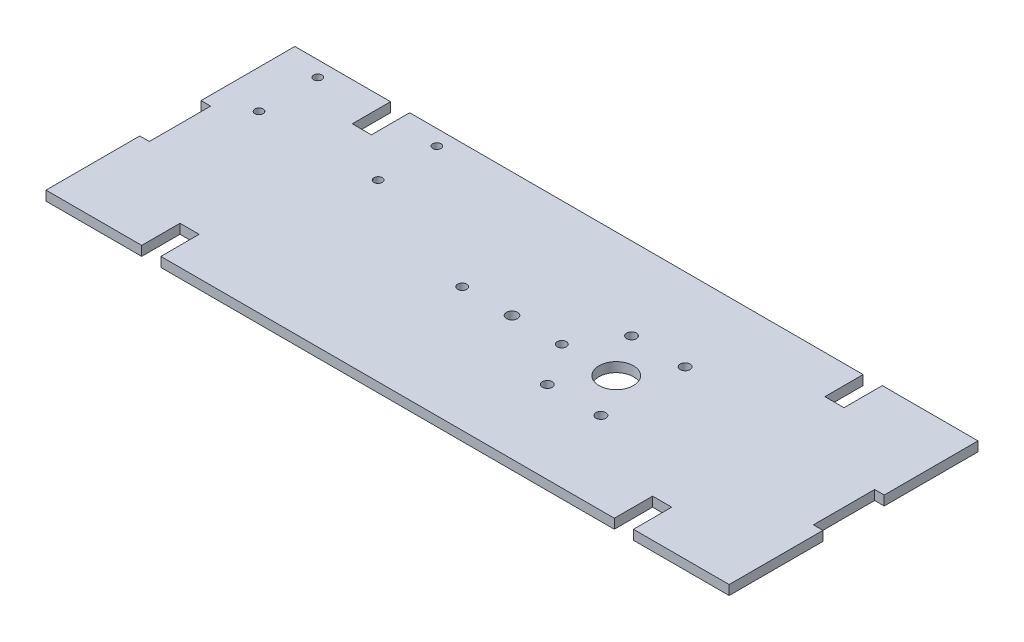
SolidWorks part; units mm, degrees
material "S-Glass Fiber"
ref_plane "Front Plane" through (0, 0, 0) normal (0, 0, 1) x (1, 0, 0)
ref_plane "Top Plane" through (0, 0, 0) normal (0, 1, 0) x (1, 0, 0)
ref_plane "Right Plane" through (0, 0, 0) normal (1, 0, 0) x (0, 0, -1)
sketch "Sketch1" plane through (0, 0, 0) normal (0, 1, 0) x (1, 0, 0)
  line L0 (-226.6315, 82.55) -> (-194.8815, 82.55)
  line L9 (-194.8815, 82.55) -> (-194.8815, 69.85)
  line L10 (-194.8815, 69.85) -> (-188.5315, 69.85)
  line L11 (-188.5315, 69.85) -> (-188.5315, 82.55)
  line L12 (-188.5315, 82.55) -> (-38.1, 82.55)
  line L13 (-38.1, 82.55) -> (-38.1, 69.85)
  line L14 (-38.1, 69.85) -> (-31.75, 69.85)
  line L15 (-31.75, 69.85) -> (-31.75, 82.55)
  line L16 (-31.75, 82.55) -> (0, 82.55)
  line L17 (0, 82.55) -> (0, 51.435)
  line L21 (0, 31.115) -> (0, 0)
  line L22 (0, 0) -> (-31.75, 0)
  line L23 (-31.75, 0) -> (-31.75, 12.7)
  line L24 (-31.75, 12.7) -> (-38.1, 12.7)
  line L25 (-38.1, 12.7) -> (-38.1, 0)
  line L26 (-38.1, 0) -> (-188.5315, 0)
  line L27 (-188.5315, 0) -> (-188.5315, 12.7)
  line L28 (-188.5315, 12.7) -> (-194.8815, 12.7)
  line L29 (-194.8815, 12.7) -> (-194.8815, 0)
  line L30 (-194.8815, 0) -> (-226.6315, 0)
  line L31 (-226.6315, 0) -> (-226.6315, 31.115)
  line L35 (-226.6315, 51.435) -> (-226.6315, 82.55)
  line L36 (-223.4565, 41.275) -> (-3.175, 41.275) construction
  line L37 (-226.6315, 51.435) -> (-223.4565, 51.435)
  line L39 (-226.6315, 31.115) -> (-223.4565, 31.115)
  line L40 (-223.4565, 51.435) -> (-223.4565, 31.115)
  line L41 (0, 51.435) -> (-3.175, 51.435)
  line L43 (0, 31.115) -> (-3.175, 31.115)
  line L44 (-3.175, 51.435) -> (-3.175, 31.115)
  line L45 (-113.3157, 82.55) -> (-113.3157, 0) construction
  circle A2 centre (-113.3158, 41.275) radius 1.8288
  dimension "D9" = 3.6576
  dimension "D1" = 82.55
  dimension "D2" = 226.6315
  dimension "D3" = 3.175
  dimension "D4" = 6.35
  dimension "D5" = 12.7
  dimension "D6" = 20.32
  dimension "D7" = 31.75
  dimension "D8" = 3.175
extrude "Boss-Extrude1" add sketch "Sketch1" along normal blind 3.175
sketch "Sketch2" plane through (0, 3.175, 0) normal (0, 1, 0) x (1, 0, 0)
  line L0 (-87.63, 55.245) -> (-69.85, 27.305) construction
  line L1 (-69.85, 55.245) -> (-87.63, 27.305) construction
  line L2 (-223.4565, 41.275) -> (-3.175, 41.275) construction
  line L3 (-223.4565, 51.435) -> (-223.4565, 31.115) construction
  line L4 (-3.175, 31.115) -> (-3.175, 51.435) construction
  line L5 (-129.8258, 41.275) -> (-96.8057, 41.275) construction
  line L6 (0, 51.435) -> (0, 82.55) construction
  circle A0 centre (-87.63, 27.305) radius 1.632
  circle A1 centre (-69.85, 27.305) radius 1.632
  circle A2 centre (-69.85, 55.245) radius 1.6319
  circle A3 centre (-87.63, 55.245) radius 1.6319
  circle A4 centre (-78.74, 41.275) radius 5.715
  circle A5 centre (-129.8258, 41.275) radius 1.524
  circle A6 centre (-96.8057, 41.275) radius 1.524
  point P25 (-113.3158, 41.275)
  point P26 (-113.3158, 41.275)
  dimension "D1" = 3.2639
  dimension "D4" = 11.43
  dimension "D6" = 3.048
  dimension "D2" = 27.94
  dimension "D3" = 17.78
  dimension "D5" = 33.02
  dimension "D7" = 78.74
extrude "Cut-Extrude1" cut sketch "Sketch2" against normal through all
sketch "Sketch3" plane through (0, 3.175, 0) normal (0, 1, 0) x (1, 0, 0)
  line L0 (-226.6315, 82.55) -> (-226.6315, 51.435) construction
  line L5 (-194.8815, 82.55) -> (-226.6315, 82.55) construction
  circle A0 centre (-174.4315, 57.97) radius 1.375
  circle A1 centre (-213.9315, 57.97) radius 1.375
  circle A2 centre (-213.9315, 77.47) radius 1.375
  circle A3 centre (-174.4315, 77.47) radius 1.375
  dimension "D3" = 2.75
  dimension "D1" = 12.7
  dimension "D2" = 5.08
  dimension "D4" = 19.5
  dimension "D5" = 39.5
extrude "Cut-Extrude2" cut sketch "Sketch3" against normal through all
